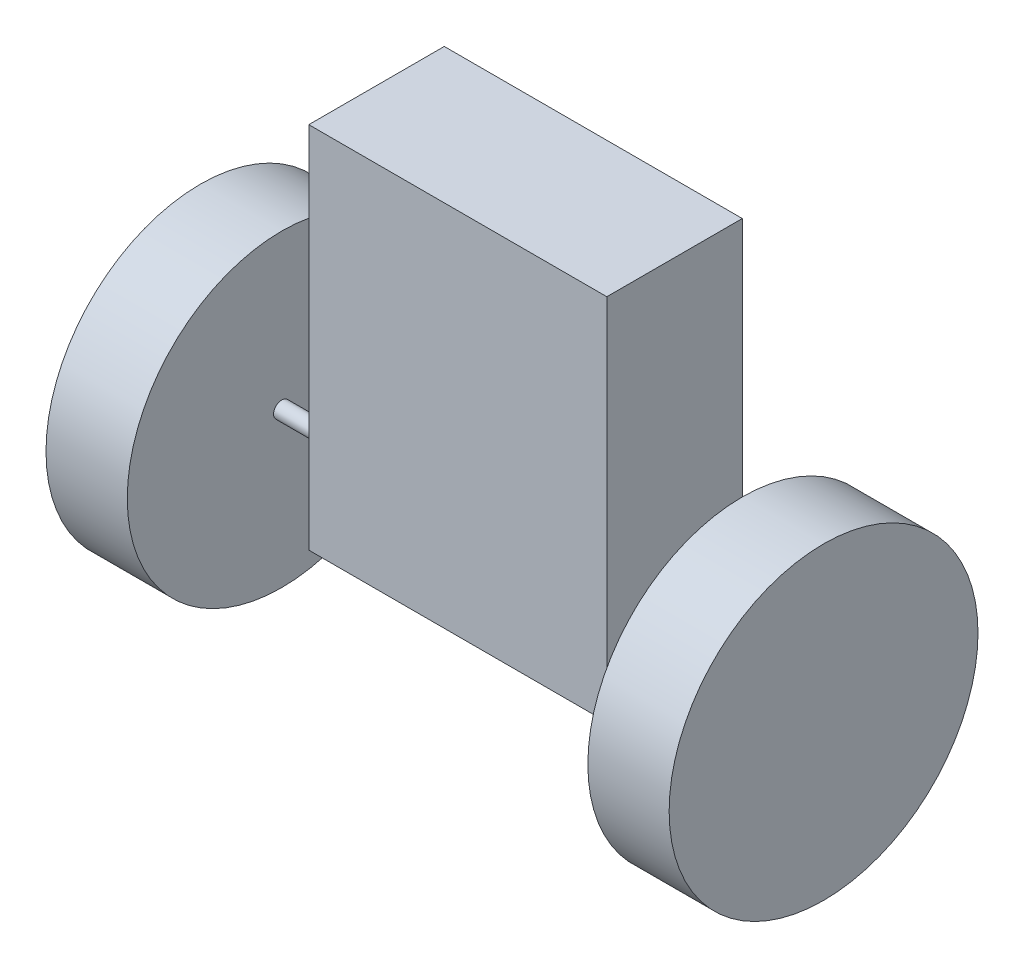
SolidWorks part; units mm, degrees
ref_plane "Plan de face" through (0, 0, 0) normal (0, 0, 1) x (1, 0, 0)
ref_plane "Plan de dessus" through (0, 0, 0) normal (0, 1, 0) x (1, 0, 0)
ref_plane "Plan de droite" through (0, 0, 0) normal (1, 0, 0) x (0, 0, -1)
sketch "Esquisse1" plane through (0, 0, 0) normal (0, 0, 1) x (1, 0, 0)
  line L1 (-27.5, -34) -> (27.5, -34)
  line L2 (-27.5, -34) -> (-27.5, 34)
  line L3 (-27.5, 34) -> (27.5, 34)
  line L4 (27.5, -34) -> (27.5, 34)
  line L5 (-27.5, -34) -> (27.5, 34) construction
  line L6 (-27.5, 34) -> (27.5, -34) construction
  point P0 (0, 0)
  dimension "D1" = 55
  dimension "D2" = 68
extrude "Boss.-Extru.1" add sketch "Esquisse1" along normal blind 25
sketch "Esquisse3" plane through (-27.5, 0, 0) normal (-1, 0, 0) x (0, 0, 1)
  line L0 (25, 34) -> (25, -34) construction
  line L1 (25, -34) -> (0, -34) construction
  circle A0 centre (15, -24) radius 1.5
  dimension "D3" = 3
  dimension "D1" = 10
  dimension "D2" = 10
extrude "Boss.-Extru.2" add sketch "Esquisse3" along normal blind 20
mirror "Symétrie1" about plane through (0, 0, 0) normal (1, 0, 0) of "Boss.-Extru.2"
sketch "Esquisse4" plane through (-47.5, 0, 0) normal (-1, 0, 0) x (0, 0, 1)
  circle A0 centre (15, -24) radius 28.5
  dimension "D1" = 57
extrude "Boss.-Extru.3" add sketch "Esquisse4" along normal blind 10 and the other way blind 5
mirror "Symétrie2" about plane through (0, 0, 0) normal (1, 0, 0) of "Boss.-Extru.3"
sketch "Esquisse5" plane through (0, 0, 0) normal (0, 0, -1) x (-1, 0, 0)
  line L0 (27.5, -23.4935) -> (32.5, -23.4935)
  line L1 (27.5, 34) -> (27.5, -34) construction
  line L2 (32.5, -23.4935) -> (32.5, -28.4935)
  line L3 (32.5, -28.4935) -> (27.5, -28.4935)
  line L4 (27.5, -28.4935) -> (27.5, -23.4935)
  dimension "D1" = 5
  dimension "D2" = 5
extrude "Boss.-Extru.4" add sketch "Esquisse5" against normal blind 2
sketch "Esquisse8" plane through (0, 0, 0) normal (0, 0, -1) x (-1, 0, 0)
  line L0 (32.5, -28.4935) -> (27.5, -23.4935) construction
  line L1 (32.5, -23.4935) -> (27.5, -28.4935) construction
hole_wizard "Dégagement M31" positions "Esquisse10" profile "Esquisse9" hole size "M3" standard "Iso"
sketch "Esquisse10" plane through (0, 0, 0) normal (0, 0, -1) x (-1, 0, 0)
  line L0 (32.5, -28.4935) -> (27.5, -23.4935) construction
  point P0 (30, -25.9935)
sketch "Esquisse9" plane through (-30, -25.9935, 0) normal (1, 0, 0) x (0, 1, 0)
  line L0 (0, 0) -> (0, 4.0215)
  line L1 (0, 4.0215) -> (1.7, 3)
  line L2 (1.7, 3) -> (1.7, 0)
  line L5 (1.7, 0) -> (0, 0)
  line L10 (0, 4.0215) -> (-1.7, 3) construction
  line L11 (0, -6.35) -> (0, 107.95) construction
  dimension "Diamètre du perçage" = 3.4
  dimension "Profondeur du perçage" = 3
  dimension "Angle de pointe" = 118
mirror "Symétrie3" about plane through (0, 0, 0) normal (1, 0, 0) of "Boss.-Extru.4", "Dégagement M31"
